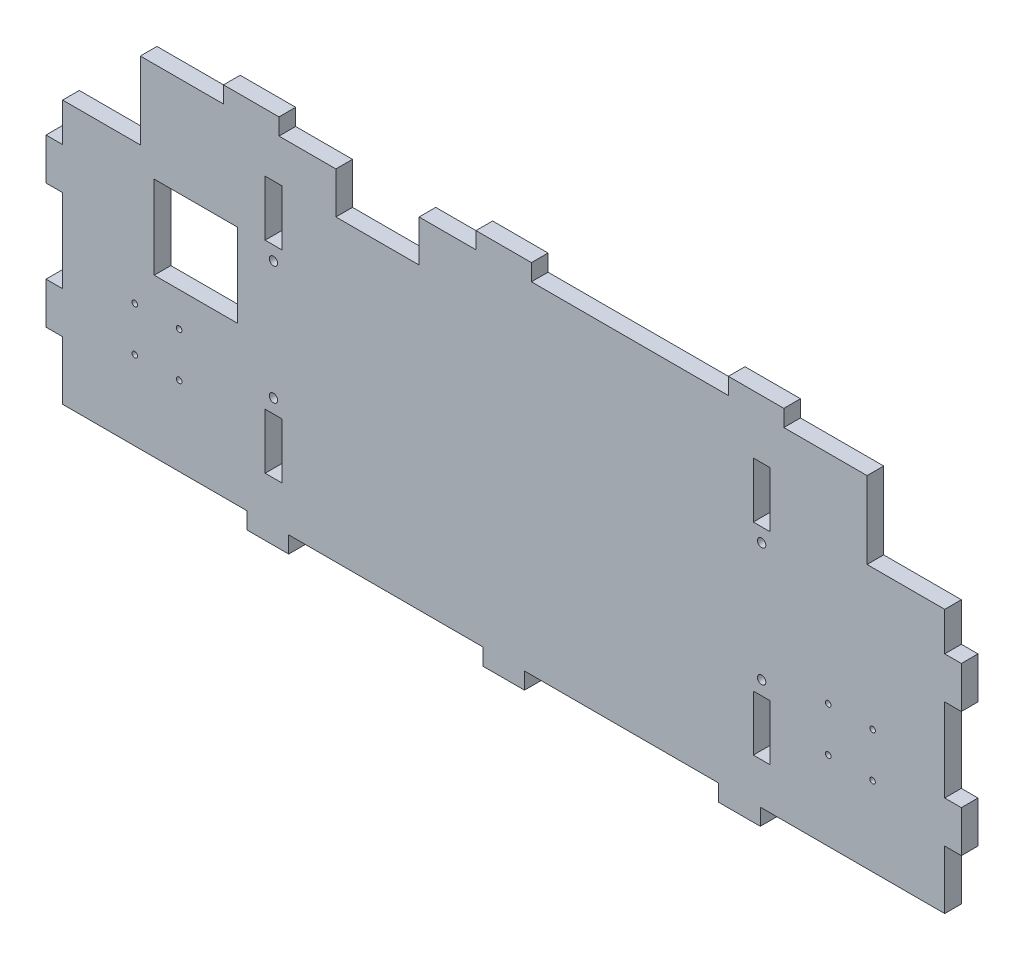
SolidWorks part; units mm, degrees
ref_plane "Plan de face" through (0, 0, 0) normal (0, 0, 1) x (1, 0, 0)
ref_plane "Plan de dessus" through (0, 0, 0) normal (0, 1, 0) x (1, 0, 0)
ref_plane "Plan de droite" through (0, 0, 0) normal (1, 0, 0) x (0, 0, -1)
sketch "Esquisse1" plane through (0, 0, 0) normal (0, 0, 1) x (1, 0, 0)
  line L0 (-159, 35) -> (-131, 35)
  line L1 (0, 102.0551) -> (0, -193.4247) construction
  line L2 (-159, 35) -> (-159, -60)
  line L3 (-159, -60) -> (159, -60)
  line L4 (159, 35) -> (159, -60)
  line L6 (131, 35) -> (131, 62.75)
  line L7 (131, 62.75) -> (-131, 62.75)
  line L8 (-131, 35) -> (-131, 62.75)
  line L9 (159, 35) -> (131, 35)
  line L10 (96, 47.75) -> (90, 47.75)
  line L11 (96, 47.75) -> (96, 27.75)
  line L12 (96, 27.75) -> (90, 27.75)
  line L13 (90, 47.75) -> (90, 27.75)
  line L14 (96, -25.01) -> (90, -25.01)
  line L15 (96, -25.01) -> (96, -45.01)
  line L16 (96, -45.01) -> (90, -45.01)
  line L17 (90, -25.01) -> (90, -45.01)
  line L18 (-80, 47.75) -> (-86, 47.75)
  line L19 (-80, 47.75) -> (-80, 27.75)
  line L20 (-80, 27.75) -> (-86, 27.75)
  line L21 (-86, 47.75) -> (-86, 27.75)
  line L22 (-80, -25.01) -> (-86, -25.01)
  line L23 (-80, -25.01) -> (-80, -45.01)
  line L24 (-80, -45.01) -> (-86, -45.01)
  line L25 (-86, -25.01) -> (-86, -45.01)
  line L26 (-95.9865, 26.8256) -> (-125.9865, 26.8256)
  line L27 (-95.9865, 26.8256) -> (-95.9865, -3.1744)
  line L28 (-95.9865, -3.1744) -> (-125.9865, -3.1744)
  line L29 (-125.9865, 26.8256) -> (-125.9865, -3.1744)
  dimension "D1" = 95
  dimension "D2" = 28
  dimension "D3" = 28
  dimension "D4" = 95
  dimension "D6" = 262
  dimension "D7" = 122.75
  dimension "D5" = 159
  dimension "D8" = 318
  dimension "D9" = 6
  dimension "D10" = 20
  dimension "D11" = 20
  dimension "D12" = 6
  dimension "D13" = 6
  dimension "D14" = 20
  dimension "D15" = 6
  dimension "D16" = 20
  dimension "D17" = 52.76
  dimension "D18" = 63
  dimension "D19" = 73
  dimension "D20" = 73
  dimension "D21" = 52.76
  dimension "D22" = 15
  dimension "D23" = 15
  dimension "D24" = 63
  dimension "D25" = 30
  dimension "D26" = 30
extrude "Boss.-Extru.1" add sketch "Esquisse1" along normal blind 6
sketch "Esquisse2" plane through (0, 0, 6) normal (0, 0, 1) x (1, 0, 0)
  line L0 (-159, -60) -> (159, -60) construction
  line L1 (-92.5, -60) -> (-77.5, -60)
  line L2 (-92.5, -60) -> (-92.5, -66)
  line L3 (-92.5, -66) -> (-77.5, -66)
  line L4 (-77.5, -60) -> (-77.5, -66)
  line L5 (-159, 35) -> (-159, -60) construction
  line L6 (-7.5, -60) -> (7.5, -60)
  line L7 (-7.5, -60) -> (-7.5, -66)
  line L8 (-7.5, -66) -> (7.5, -66)
  line L9 (7.5, -60) -> (7.5, -66)
  line L10 (77.5, -60) -> (92.5, -60)
  line L11 (77.5, -60) -> (77.5, -66)
  line L12 (77.5, -66) -> (92.5, -66)
  line L13 (92.5, -60) -> (92.5, -66)
  line L14 (176.2958, 0) -> (-249.7093, -3.2925) construction
  line L15 (0, 107.6082) -> (0, -117.4775) construction
  line L16 (-131, 35) -> (-159, 35) construction
  line L17 (-159, 21.09) -> (-165, 21.09)
  line L18 (-159, 21.09) -> (-159, 6.09)
  line L19 (-159, 6.09) -> (-165, 6.09)
  line L20 (-165, 21.09) -> (-165, 6.09)
  line L21 (-159, -23.91) -> (-165, -23.91)
  line L22 (-159, -23.91) -> (-159, -38.91)
  line L23 (-159, -38.91) -> (-165, -38.91)
  line L24 (-165, -23.91) -> (-165, -38.91)
  line L25 (165, -23.91) -> (165, -38.91)
  line L26 (159, -38.91) -> (165, -38.91)
  line L27 (159, -23.91) -> (159, -38.91)
  line L28 (159, -23.91) -> (165, -23.91)
  line L29 (165, 21.09) -> (165, 6.09)
  line L30 (159, 6.09) -> (165, 6.09)
  line L31 (159, 21.09) -> (159, 6.09)
  line L32 (159, 21.09) -> (165, 21.09)
  line L33 (131, 62.75) -> (-131, 62.75) construction
  line L34 (101, 62.75) -> (81, 62.75)
  line L35 (101, 62.75) -> (101, 68.75)
  line L36 (101, 68.75) -> (81, 68.75)
  line L37 (81, 62.75) -> (81, 68.75)
  line L38 (-131, 62.75) -> (-131, 35) construction
  line L39 (-81, 62.75) -> (-101, 62.75)
  line L40 (-81, 62.75) -> (-81, 68.75)
  line L41 (-81, 68.75) -> (-101, 68.75)
  line L42 (-101, 62.75) -> (-101, 68.75)
  line L43 (10, 62.75) -> (-10, 62.75)
  line L44 (10, 62.75) -> (10, 68.75)
  line L45 (10, 68.75) -> (-10, 68.75)
  line L46 (-10, 62.75) -> (-10, 68.75)
  line L47 (131, 35) -> (131, 62.75) construction
  dimension "D1" = 66.5
  dimension "D2" = 70
  dimension "D3" = 15
  dimension "D4" = 15
  dimension "D5" = 70
  dimension "D6" = 15
  dimension "D7" = 6
  dimension "D8" = 6
  dimension "D9" = 6
  dimension "D10" = 6
  dimension "D11" = 13.91
  dimension "D12" = 15
  dimension "D13" = 30
  dimension "D14" = 15
  dimension "D15" = 20
  dimension "D16" = 20
  dimension "D17" = 20
  dimension "D18" = 30
  dimension "D19" = 30
  dimension "D20" = 121
  dimension "D21" = 6
  dimension "D22" = 6
  dimension "D23" = 6
  dimension "D24" = 6
extrude "Boss.-Extru.2" add sketch "Esquisse2" against normal blind 6
sketch "Esquisse3" plane through (0, 0, 0) normal (0, 0, -1) x (-1, 0, 0)
  line L2 (0, 141.59) -> (0, -167.3887) construction
  line L3 (83, 57.185) -> (83, -52.5738) construction
  line L4 (-93, 52.3657) -> (-93, -53.0892) construction
  line L5 (-90, 27.75) -> (-96, 27.75) construction
  line L6 (-96, 27.75) -> (-96, 47.75) construction
  line L7 (-96, -25.01) -> (-90, -25.01) construction
  line L8 (80, -25.01) -> (86, -25.01) construction
  line L9 (80, -45.01) -> (80, -25.01) construction
  line L10 (86, 27.75) -> (80, 27.75) construction
  line L11 (159, 6.09) -> (159, -23.91) construction
  line L12 (117, -15.49) -> (133, -15.49) construction
  line L13 (117, -15.49) -> (117, -31.49) construction
  line L14 (117, -31.49) -> (133, -31.49) construction
  line L15 (133, -15.49) -> (133, -31.49) construction
  line L16 (159, -60) -> (92.5, -60) construction
  circle A0 centre (133, -31.49) radius 1
  circle A1 centre (133, -15.49) radius 1
  circle A2 centre (117, -15.49) radius 1
  circle A3 centre (117, -31.49) radius 1
  circle A4 centre (-117, -31.49) radius 1
  circle A5 centre (-117, -15.49) radius 1
  circle A6 centre (-133, -15.49) radius 1
  circle A7 centre (-133, -31.49) radius 1
  circle A9 centre (83, 22.75) radius 1.5
  circle A10 centre (83, -20.01) radius 1.5
  circle A13 centre (-93, 22.75) radius 1.5
  circle A14 centre (-93, -20.01) radius 1.5
  dimension "D7" = 2
  dimension "D8" = 2
  dimension "D9" = 2
  dimension "D10" = 2
  dimension "D11" = 3
  dimension "D12" = 3
  dimension "D13" = 3
  dimension "D14" = 3
  dimension "D17" = 5
  dimension "D18" = 5
  dimension "D20" = 5
  dimension "D3" = 16
  dimension "D4" = 26
  dimension "D5" = 28.51
  dimension "D15" = 5
  dimension "D16" = 3
  dimension "D19" = 3
extrude "Enlèv. mat.-Extru.1" cut sketch "Esquisse3" against normal blind 6
sketch "Esquisse4" plane through (0, 0, 0) normal (0, 0, -1) x (-1, 0, 0)
  line L0 (10, 62.75) -> (81, 62.75) construction
  line L1 (30.5, 62.75) -> (60.5, 62.75)
  line L2 (30.5, 62.75) -> (30.5, 47.75)
  line L3 (30.5, 47.75) -> (60.5, 47.75)
  line L4 (60.5, 62.75) -> (60.5, 47.75)
  line L5 (10, 68.75) -> (10, 62.75) construction
  dimension "D1" = 20.5
  dimension "D2" = 30
  dimension "D3" = 15
extrude "Enlèv. mat.-Extru.2" cut sketch "Esquisse4" against normal blind 6
equation "\"D5@Esquisse1\"=\"D8@Esquisse1\"/2"
